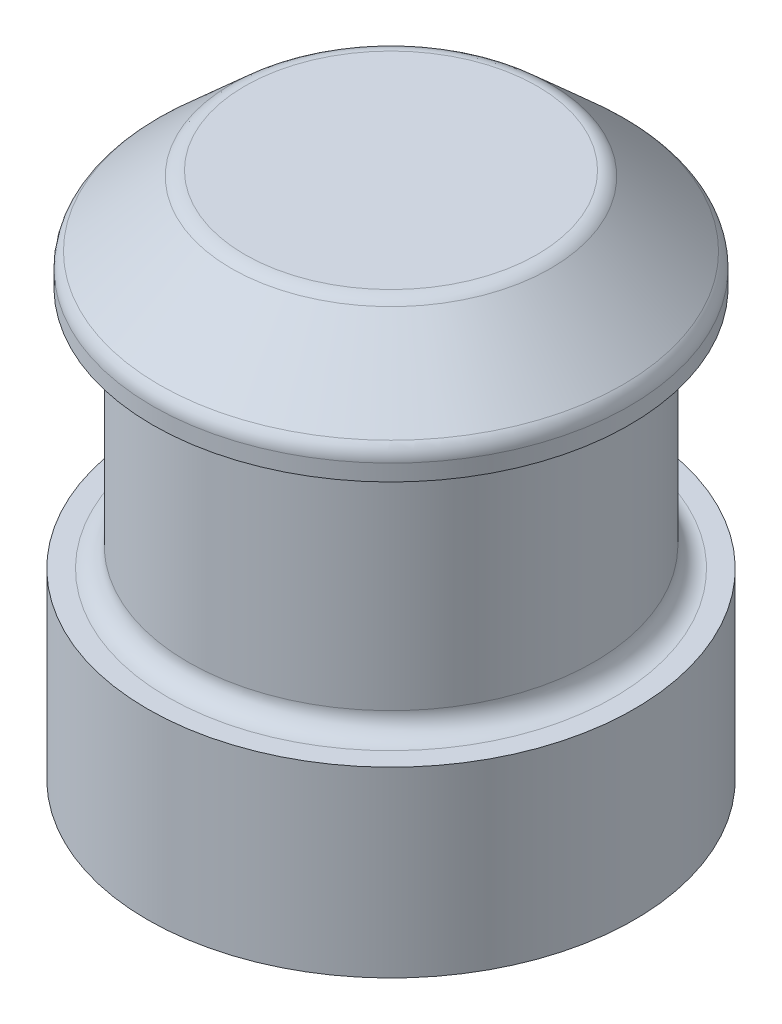
SolidWorks part; units mm, degrees
ref_plane "Front Plane" through (0, 0, 0) normal (0, 0, 1) x (1, 0, 0)
ref_plane "Top Plane" through (0, 0, 0) normal (0, 1, 0) x (1, 0, 0)
ref_plane "Right Plane" through (0, 0, 0) normal (1, 0, 0) x (0, 0, -1)
sketch "Sketch1" plane through (0, 0, 0) normal (0, 1, 0) x (1, 0, 0)
  line L5 (7, -7) -> (-7, 7) construction
  line L6 (7, 7) -> (-7, -7) construction
  circle A0 centre (0, 0) radius 2.4
  point P0 (0, 0)
  dimension "D3" = 4.8
  dimension "D1" = 14
  dimension "D2" = 14
extrude "Boss-Extrude1" add sketch "Sketch1" along normal blind 1.8
ref_plane "Plane1" through (0, 1.8, 0) normal (0, 1, 0) x (1, 0, 0)
sketch "Sketch2" plane through (0, 1.8, 0) normal (0, 1, 0) x (1, 0, 0)
  circle A0 centre (0, 0) radius 2
extrude "Boss-Extrude2" add sketch "Sketch2" along normal blind 2.4
ref_plane "Plane2" through (0, 4.2, 0) normal (0, 1, 0) x (1, 0, 0)
sketch "Sketch3" plane through (0, 4.2, 0) normal (0, 1, 0) x (1, 0, 0)
  circle A0 centre (0, 0) radius 2.35
  circle A1 centre (0, 0) radius 2 construction
extrude "Boss-Extrude3" add sketch "Sketch3" along normal blind 1
chamfer "Chamfer1" distance 0.75 angle 48 1 edges at (0, 5.2, 2.35)
fillet "Fillet1" radius 0.2 3 edges at (0, 5.2, 1.517) (0, 4.45, 2.35) (0, 1.8, 2)
scale "Scale1" scale about centroid uniform scaling yes scale factor 1.15
